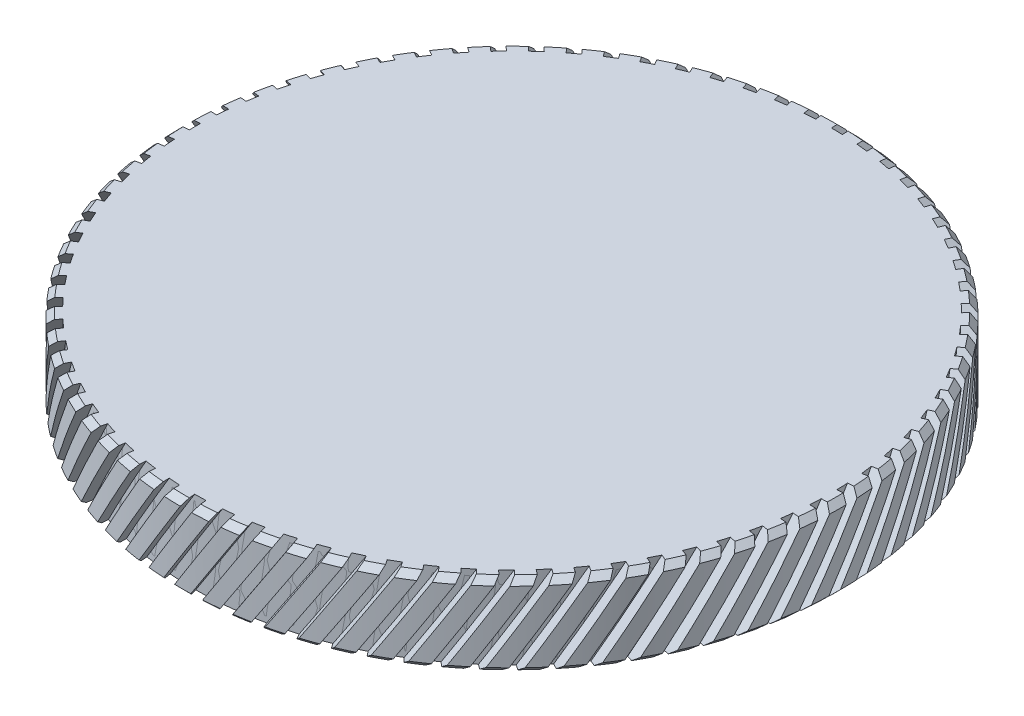
SolidWorks part; units mm, degrees
ref_plane "前视基准面" through (0, 0, 0) normal (0, 0, 1) x (1, 0, 0)
ref_plane "上视基准面" through (0, 0, 0) normal (0, 1, 0) x (1, 0, 0)
ref_plane "右视基准面" through (0, 0, 0) normal (1, 0, 0) x (0, 0, -1)
sketch "草图1" plane through (0, 0, 0) normal (0, 0, 1) x (1, 0, 0)
  line L0 (0, 46.0207) -> (0, -69.6142) construction
  line L1 (25.1, -8.8309) -> (26.1, -8.8309)
  line L2 (28, -6.3309) -> (0, -6.3309)
  line L3 (25.1, -13.3309) -> (28, -13.3309)
  line L4 (25.1, -13.3309) -> (25.1, -8.8309)
  line L5 (26.1, -8.8309) -> (26.1, -7.8309)
  line L6 (28, -13.3309) -> (28, -6.3309)
  line L7 (26.1, -7.8309) -> (0, -7.8309)
  line L8 (0, -7.8309) -> (0, -6.3309)
  dimension "D1" = 26.1
  dimension "D2" = 7
  dimension "D3" = 28
  dimension "D4" = 25.1
  dimension "D5" = 4.5
  dimension "D6" = 5.5
revolve "旋转1" add sketch "草图1" angle 360 about L0
cosmetic thread "装饰螺纹线1" parameters "D1"=2.5, "D2"=52
chamfer "倒角1" distance 0.5 angle 45 2 edges at (0, -6.3309, 28) (0, -13.3309, 28)
surface "曲面-等距1" parameters "D1"=1
sketch "草图2" plane through (0, 0, 0) normal (0, 0, 1) x (1, 0, 0)
  line L0 (0, -2.7759) -> (-6.5923, -13.3309)
  line L1 (0, -2.7759) -> (0.6785, -3.1997)
  line L2 (-6.5923, -13.3309) -> (-5.9138, -13.7547)
  line L3 (0.6785, -3.1997) -> (-5.9138, -13.7547)
  line L4 (-27.5, -13.3309) -> (27.5, -13.3309) construction
extrude "切除-拉伸1" cut sketch "草图2" against normal up to surface (3 mm away) from offset 30
pattern_circular "阵列(圆周)1" count 75 over 360 about axis through (0, 0, 0) along (0, 1, 0) of "切除-拉伸1"
